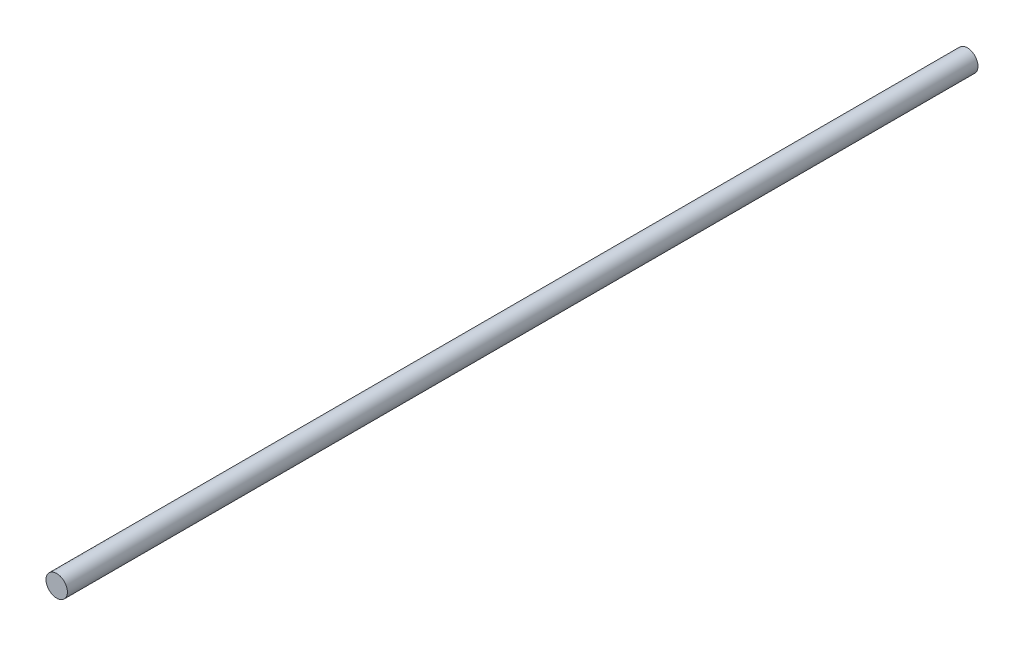
SolidWorks part; units mm, degrees
ref_plane "Plan de face" through (0, 0, 0) normal (0, 0, 1) x (1, 0, 0)
ref_plane "Plan de dessus" through (0, 0, 0) normal (0, 1, 0) x (1, 0, 0)
ref_plane "Plan de droite" through (0, 0, 0) normal (1, 0, 0) x (0, 0, -1)
sketch "Esquisse1" plane through (0, 0, 0) normal (0, 0, 1) x (1, 0, 0)
  circle A0 centre (0, 0) radius 1
  dimension "D1" = 2
extrude "Boss.-Extru.1" add sketch "Esquisse1" along normal blind 85
